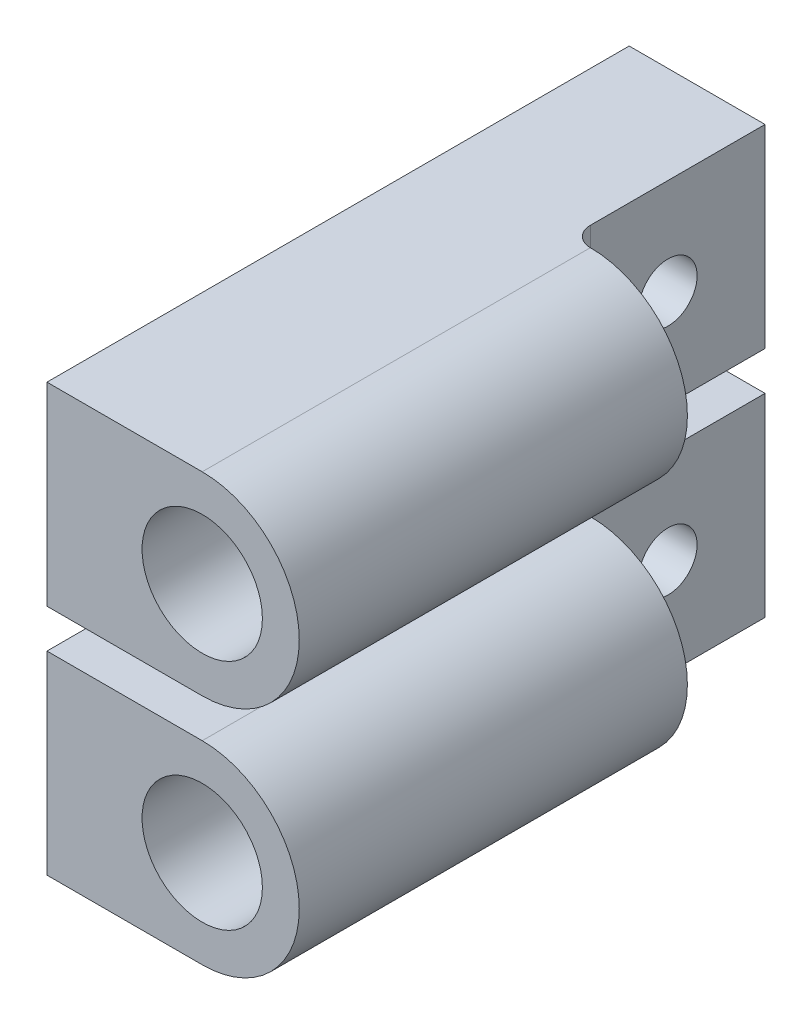
SolidWorks part; units mm, degrees
ref_plane "Front Plane" through (0, 0, 0) normal (0, 0, 1) x (1, 0, 0)
ref_plane "Top Plane" through (0, 0, 0) normal (0, 1, 0) x (1, 0, 0)
ref_plane "Right Plane" through (0, 0, 0) normal (1, 0, 0) x (0, 0, -1)
sketch "Sketch1" plane through (0, 0, 0) normal (0, 0, 1) x (1, 0, 0)
  line L0 (-8, 5) -> (-8, -5)
  line L5 (-8, -5) -> (0, -5)
  line L6 (-8, 5) -> (0, 5)
  arc A0 (0, -5) -> (0, 5) centre (0, 0) ccw
  dimension "D1" = 10
  dimension "D4" = 8
extrude "Main" add sketch "Sketch1" along normal blind 30
ref_plane "Plane1" through (-1, 0, 0) normal (-1, 0, 0) x (0, 0, 1)
sketch "Sketch2" plane through (0, 0, 30) normal (0, 0, 1) x (1, 0, 0)
  circle A0 centre (0, 0) radius 3.1
  dimension "D1" = 6.2
extrude "ShaftHole" cut sketch "Sketch2" against normal blind 16
sketch "Sketch3" plane through (-1, 0, 0) normal (1, 0, 0) x (0, 0, -1)
  line L0 (-30, 5) -> (0, 5) construction
  line L1 (-10, 5) -> (0, 5)
  line L2 (-10, 5) -> (-10, -5)
  line L3 (-10, -5) -> (0, -5)
  line L4 (0, 5) -> (0, -5)
  line L5 (-30, -5) -> (0, -5) construction
  line L6 (0, -5) -> (0, 5) construction
  dimension "D1" = 10
extrude "MakerBeamRectangularHole" cut sketch "Sketch3" along normal through all
sketch "Sketch4" plane through (-1, 0, 0) normal (1, 0, 0) x (0, 0, -1)
  line L0 (0, -5) -> (0, 5) construction
  circle A0 centre (-5, 0) radius 1.5
  dimension "D1" = 3
  dimension "D2" = 5
extrude "MakerBeamHole" cut sketch "Sketch4" against normal through all
fillet "Fillet1" radius 1 1 edges at (-1, 0, 10)
pattern_linear "LPattern1" count 2 spacing 12 along (0, 1, 0) of bodies 104
